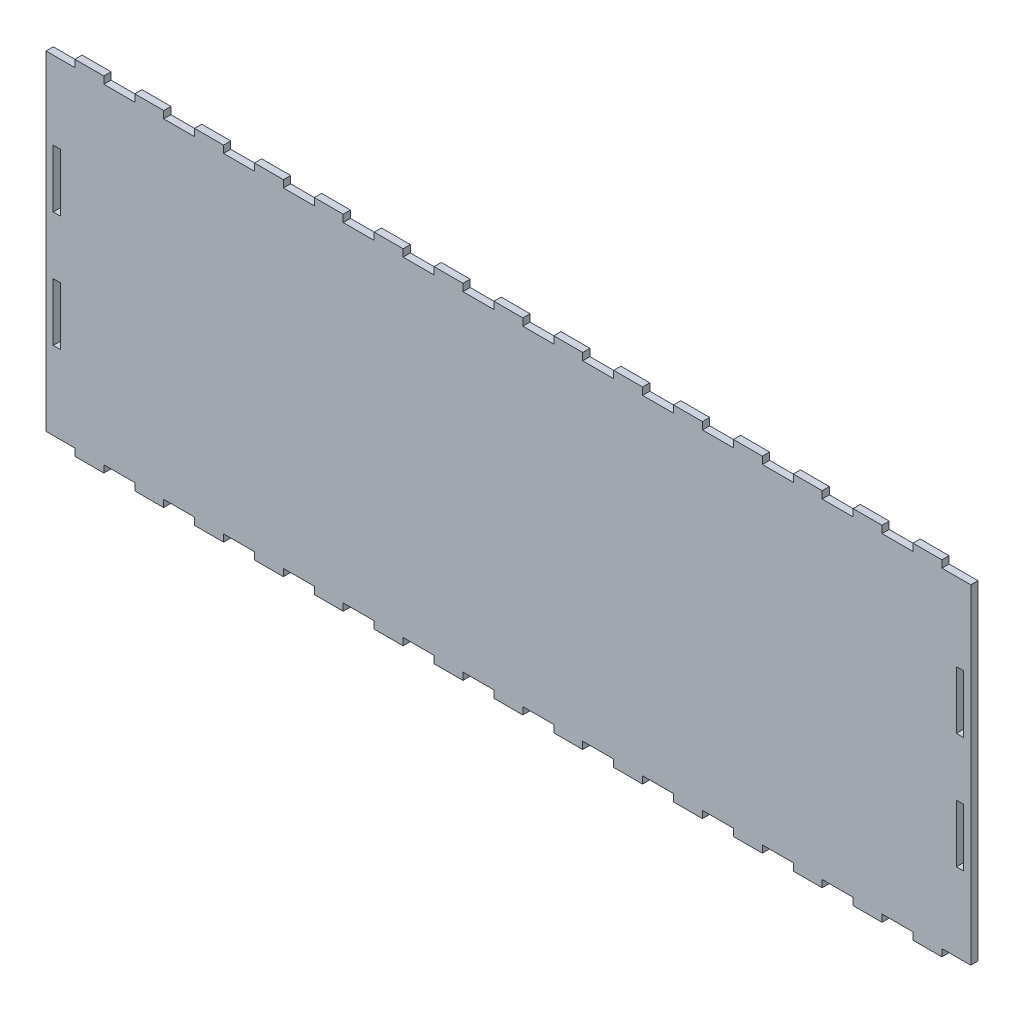
SolidWorks part; units mm, degrees
ref_plane "Front Plane" through (0, 0, 0) normal (0, 0, 1) x (1, 0, 0)
ref_plane "Top Plane" through (0, 0, 0) normal (0, 1, 0) x (1, 0, 0)
ref_plane "Right Plane" through (0, 0, 0) normal (1, 0, 0) x (0, 0, -1)
sketch "Sketch1" plane through (0, 0, 0) normal (0, 0, 1) x (1, 0, 0)
  line L8 (400.05, 110.49) -> (400.05, 85.09)
  line L9 (403.225, 110.49) -> (400.05, 110.49)
  line L10 (403.225, 85.09) -> (403.225, 110.49)
  line L11 (400.05, 85.09) -> (403.225, 85.09)
  line L16 (6.35, 34.29) -> (6.35, 59.69)
  line L17 (3.175, 34.29) -> (6.35, 34.29)
  line L18 (3.175, 59.69) -> (3.175, 34.29)
  line L19 (6.35, 59.69) -> (3.175, 59.69)
  line L24 (6.35, 85.09) -> (6.35, 110.49)
  line L25 (3.175, 85.09) -> (6.35, 85.09)
  line L26 (3.175, 110.49) -> (3.175, 85.09)
  line L27 (6.35, 110.49) -> (3.175, 110.49)
  line L32 (400.05, 59.69) -> (400.05, 34.29)
  line L33 (403.225, 59.69) -> (400.05, 59.69)
  line L34 (403.225, 34.29) -> (403.225, 59.69)
  line L35 (400.05, 34.29) -> (403.225, 34.29)
  line L280 (406.4, 0) -> (406.4, 144.78)
  line L281 (406.4, 144.78) -> (393.7, 144.78)
  line L282 (393.7, 144.78) -> (393.7, 147.955)
  line L283 (393.7, 147.955) -> (381, 147.955)
  line L284 (381, 147.955) -> (381, 144.78)
  line L285 (381, 144.78) -> (367.3929, 144.78)
  line L286 (367.3929, 144.78) -> (367.3929, 147.955)
  line L287 (367.3929, 147.955) -> (354.6929, 147.955)
  line L288 (354.6929, 147.955) -> (354.6929, 144.78)
  line L289 (354.6929, 144.78) -> (341.0857, 144.78)
  line L290 (341.0857, 144.78) -> (341.0857, 147.955)
  line L291 (341.0857, 147.955) -> (328.3857, 147.955)
  line L292 (328.3857, 147.955) -> (328.3857, 144.78)
  line L293 (328.3857, 144.78) -> (314.7786, 144.78)
  line L294 (314.7786, 144.78) -> (314.7786, 147.955)
  line L295 (314.7786, 147.955) -> (302.0786, 147.955)
  line L296 (302.0786, 147.955) -> (302.0786, 144.78)
  line L297 (302.0786, 144.78) -> (288.4714, 144.78)
  line L298 (288.4714, 144.78) -> (288.4714, 147.955)
  line L299 (288.4714, 147.955) -> (275.7714, 147.955)
  line L300 (275.7714, 147.955) -> (275.7714, 144.78)
  line L301 (275.7714, 144.78) -> (262.1643, 144.78)
  line L302 (262.1643, 144.78) -> (262.1643, 147.955)
  line L303 (262.1643, 147.955) -> (249.4643, 147.955)
  line L304 (249.4643, 147.955) -> (249.4643, 144.78)
  line L305 (249.4643, 144.78) -> (235.8571, 144.78)
  line L306 (235.8571, 144.78) -> (235.8571, 147.955)
  line L307 (235.8571, 147.955) -> (223.1571, 147.955)
  line L308 (223.1571, 147.955) -> (223.1571, 144.78)
  line L309 (223.1571, 144.78) -> (209.55, 144.78)
  line L310 (209.55, 144.78) -> (209.55, 147.955)
  line L311 (209.55, 147.955) -> (196.85, 147.955)
  line L312 (196.85, 147.955) -> (196.85, 144.78)
  line L313 (196.85, 144.78) -> (183.2429, 144.78)
  line L314 (183.2429, 144.78) -> (183.2429, 147.955)
  line L315 (183.2429, 147.955) -> (170.5429, 147.955)
  line L316 (170.5429, 147.955) -> (170.5429, 144.78)
  line L317 (170.5429, 144.78) -> (156.9357, 144.78)
  line L318 (156.9357, 144.78) -> (156.9357, 147.955)
  line L319 (156.9357, 147.955) -> (144.2357, 147.955)
  line L320 (144.2357, 147.955) -> (144.2357, 144.78)
  line L321 (144.2357, 144.78) -> (130.6286, 144.78)
  line L322 (130.6286, 144.78) -> (130.6286, 147.955)
  line L323 (130.6286, 147.955) -> (117.9286, 147.955)
  line L324 (117.9286, 147.955) -> (117.9286, 144.78)
  line L325 (117.9286, 144.78) -> (104.3214, 144.78)
  line L326 (104.3214, 144.78) -> (104.3214, 147.955)
  line L327 (104.3214, 147.955) -> (91.6214, 147.955)
  line L328 (91.6214, 147.955) -> (91.6214, 144.78)
  line L329 (91.6214, 144.78) -> (78.0143, 144.78)
  line L330 (78.0143, 144.78) -> (78.0143, 147.955)
  line L331 (78.0143, 147.955) -> (65.3143, 147.955)
  line L332 (65.3143, 147.955) -> (65.3143, 144.78)
  line L333 (65.3143, 144.78) -> (51.7071, 144.78)
  line L334 (51.7071, 144.78) -> (51.7071, 147.955)
  line L335 (51.7071, 147.955) -> (39.0071, 147.955)
  line L336 (39.0071, 147.955) -> (39.0071, 144.78)
  line L337 (39.0071, 144.78) -> (25.4, 144.78)
  line L338 (25.4, 144.78) -> (25.4, 147.955)
  line L339 (25.4, 147.955) -> (12.7, 147.955)
  line L340 (12.7, 147.955) -> (12.7, 144.78)
  line L341 (12.7, 144.78) -> (0, 144.78)
  line L342 (0, 144.78) -> (0, 0)
  line L343 (0, 0) -> (12.7, 0)
  line L344 (12.7, 0) -> (12.7, -3.175)
  line L345 (12.7, -3.175) -> (25.4, -3.175)
  line L346 (25.4, -3.175) -> (25.4, 0)
  line L347 (25.4, 0) -> (39.0071, 0)
  line L348 (39.0071, 0) -> (39.0071, -3.175)
  line L349 (39.0071, -3.175) -> (51.7071, -3.175)
  line L350 (51.7071, -3.175) -> (51.7071, 0)
  line L351 (51.7071, 0) -> (65.3143, 0)
  line L352 (65.3143, 0) -> (65.3143, -3.175)
  line L353 (65.3143, -3.175) -> (78.0143, -3.175)
  line L354 (78.0143, -3.175) -> (78.0143, 0)
  line L355 (78.0143, 0) -> (91.6214, 0)
  line L356 (91.6214, 0) -> (91.6214, -3.175)
  line L357 (91.6214, -3.175) -> (104.3214, -3.175)
  line L358 (104.3214, -3.175) -> (104.3214, 0)
  line L359 (104.3214, 0) -> (117.9286, 0)
  line L360 (117.9286, 0) -> (117.9286, -3.175)
  line L361 (117.9286, -3.175) -> (130.6286, -3.175)
  line L362 (130.6286, -3.175) -> (130.6286, 0)
  line L363 (130.6286, 0) -> (144.2357, 0)
  line L364 (144.2357, 0) -> (144.2357, -3.175)
  line L365 (144.2357, -3.175) -> (156.9357, -3.175)
  line L366 (156.9357, -3.175) -> (156.9357, 0)
  line L367 (156.9357, 0) -> (170.5429, 0)
  line L368 (170.5429, 0) -> (170.5429, -3.175)
  line L369 (170.5429, -3.175) -> (183.2429, -3.175)
  line L370 (183.2429, -3.175) -> (183.2429, 0)
  line L371 (183.2429, 0) -> (196.85, 0)
  line L372 (196.85, 0) -> (196.85, -3.175)
  line L373 (196.85, -3.175) -> (209.55, -3.175)
  line L374 (209.55, -3.175) -> (209.55, 0)
  line L375 (209.55, 0) -> (223.1571, 0)
  line L376 (223.1571, 0) -> (223.1571, -3.175)
  line L377 (223.1571, -3.175) -> (235.8571, -3.175)
  line L378 (235.8571, -3.175) -> (235.8571, 0)
  line L379 (235.8571, 0) -> (249.4643, 0)
  line L380 (249.4643, 0) -> (249.4643, -3.175)
  line L381 (249.4643, -3.175) -> (262.1643, -3.175)
  line L382 (262.1643, -3.175) -> (262.1643, 0)
  line L383 (262.1643, 0) -> (275.7714, 0)
  line L384 (275.7714, 0) -> (275.7714, -3.175)
  line L385 (275.7714, -3.175) -> (288.4714, -3.175)
  line L386 (288.4714, -3.175) -> (288.4714, 0)
  line L387 (288.4714, 0) -> (302.0786, 0)
  line L388 (302.0786, 0) -> (302.0786, -3.175)
  line L389 (302.0786, -3.175) -> (314.7786, -3.175)
  line L390 (314.7786, -3.175) -> (314.7786, 0)
  line L391 (314.7786, 0) -> (328.3857, 0)
  line L392 (328.3857, 0) -> (328.3857, -3.175)
  line L393 (328.3857, -3.175) -> (341.0857, -3.175)
  line L394 (341.0857, -3.175) -> (341.0857, 0)
  line L395 (341.0857, 0) -> (354.6929, 0)
  line L396 (354.6929, 0) -> (354.6929, -3.175)
  line L397 (354.6929, -3.175) -> (367.3929, -3.175)
  line L398 (367.3929, -3.175) -> (367.3929, 0)
  line L399 (367.3929, 0) -> (381, 0)
  line L400 (381, 0) -> (381, -3.175)
  line L401 (381, -3.175) -> (393.7, -3.175)
  line L402 (393.7, -3.175) -> (393.7, 0)
  line L403 (393.7, 0) -> (406.4, 0)
extrude "Boss-Extrude1" add sketch "Sketch1" along normal blind 3.175
sketch "DXF" plane through (0, 0, 3.175) normal (0, 0, 1) x (1, 0, 0)
  line L192 (400.1516, 85.1916) -> (403.1234, 85.1916)
  line L193 (403.1234, 85.1916) -> (403.1234, 110.3884)
  line L194 (400.1516, 110.3884) -> (400.1516, 85.1916)
  line L195 (403.1234, 110.3884) -> (400.1516, 110.3884)
  line L196 (400.1516, 85.1916) -> (403.1234, 85.1916)
  line L197 (403.1234, 85.1916) -> (403.1234, 110.3884)
  line L198 (400.1516, 110.3884) -> (400.1516, 85.1916)
  line L199 (403.1234, 110.3884) -> (400.1516, 110.3884)
  line L210 (400.1516, 34.3916) -> (403.1234, 34.3916)
  line L211 (403.1234, 34.3916) -> (403.1234, 59.5884)
  line L212 (403.1234, 59.5884) -> (400.1516, 59.5884)
  line L213 (400.1516, 59.5884) -> (400.1516, 34.3916)
  line L214 (400.1516, 34.3916) -> (403.1234, 34.3916)
  line L215 (403.1234, 34.3916) -> (403.1234, 59.5884)
  line L216 (403.1234, 59.5884) -> (400.1516, 59.5884)
  line L217 (400.1516, 59.5884) -> (400.1516, 34.3916)
  line L292 (3.2766, 85.1916) -> (6.2484, 85.1916)
  line L293 (6.2484, 85.1916) -> (6.2484, 110.3884)
  line L294 (6.2484, 110.3884) -> (3.2766, 110.3884)
  line L295 (3.2766, 110.3884) -> (3.2766, 85.1916)
  line L296 (3.2766, 85.1916) -> (6.2484, 85.1916)
  line L297 (6.2484, 85.1916) -> (6.2484, 110.3884)
  line L298 (6.2484, 110.3884) -> (3.2766, 110.3884)
  line L299 (3.2766, 110.3884) -> (3.2766, 85.1916)
  line L310 (3.0734, 34.1884) -> (6.4516, 34.1884)
  line L311 (6.4516, 34.1884) -> (6.4516, 59.7916)
  line L312 (3.0734, 59.7916) -> (3.0734, 34.1884)
  line L313 (6.4516, 59.7916) -> (3.0734, 59.7916)
  line L314 (3.0734, 34.1884) -> (6.4516, 34.1884)
  line L315 (6.4516, 34.1884) -> (6.4516, 59.7916)
  line L316 (3.0734, 59.7916) -> (3.0734, 34.1884)
  line L317 (6.4516, 59.7916) -> (3.0734, 59.7916)
  line L372 (393.8016, -0.1016) -> (406.5016, -0.1016)
  line L373 (406.5016, -0.1016) -> (406.5016, 144.8816)
  line L374 (406.5016, 144.8816) -> (393.8016, 144.8816)
  line L375 (393.8016, 144.8816) -> (393.8016, 148.0566)
  line L376 (393.8016, 148.0566) -> (380.8984, 148.0566)
  line L377 (380.8984, 148.0566) -> (380.8984, 144.8816)
  line L378 (380.8984, 144.8816) -> (367.4945, 144.8816)
  line L379 (367.4945, 144.8816) -> (367.4945, 148.0566)
  line L380 (367.4945, 148.0566) -> (354.5913, 148.0566)
  line L381 (354.5913, 148.0566) -> (354.5913, 144.8816)
  line L382 (354.5913, 144.8816) -> (341.1873, 144.8816)
  line L383 (341.1873, 144.8816) -> (341.1873, 148.0566)
  line L384 (341.1873, 148.0566) -> (328.2841, 148.0566)
  line L385 (328.2841, 148.0566) -> (328.2841, 144.8816)
  line L386 (328.2841, 144.8816) -> (314.8802, 144.8816)
  line L387 (314.8802, 144.8816) -> (314.8802, 148.0566)
  line L388 (314.8802, 148.0566) -> (301.977, 148.0566)
  line L389 (301.977, 148.0566) -> (301.977, 144.8816)
  line L390 (301.977, 144.8816) -> (288.573, 144.8816)
  line L391 (288.573, 144.8816) -> (288.573, 148.0566)
  line L392 (288.573, 148.0566) -> (275.6698, 148.0566)
  line L393 (275.6698, 148.0566) -> (275.6698, 144.8816)
  line L394 (275.6698, 144.8816) -> (262.2659, 144.8816)
  line L395 (262.2659, 144.8816) -> (262.2659, 148.0566)
  line L396 (262.2659, 148.0566) -> (249.3627, 148.0566)
  line L397 (249.3627, 148.0566) -> (249.3627, 144.8816)
  line L398 (249.3627, 144.8816) -> (235.9587, 144.8816)
  line L399 (235.9587, 144.8816) -> (235.9587, 148.0566)
  line L400 (235.9587, 148.0566) -> (223.0555, 148.0566)
  line L401 (223.0555, 148.0566) -> (223.0555, 144.8816)
  line L402 (223.0555, 144.8816) -> (209.6516, 144.8816)
  line L403 (209.6516, 144.8816) -> (209.6516, 148.0566)
  line L404 (209.6516, 148.0566) -> (196.7484, 148.0566)
  line L405 (196.7484, 148.0566) -> (196.7484, 144.8816)
  line L406 (196.7484, 144.8816) -> (183.3445, 144.8816)
  line L407 (183.3445, 144.8816) -> (183.3445, 148.0566)
  line L408 (183.3445, 148.0566) -> (170.4413, 148.0566)
  line L409 (170.4413, 148.0566) -> (170.4413, 144.8816)
  line L410 (170.4413, 144.8816) -> (157.0373, 144.8816)
  line L411 (157.0373, 144.8816) -> (157.0373, 148.0566)
  line L412 (157.0373, 148.0566) -> (144.1341, 148.0566)
  line L413 (144.1341, 148.0566) -> (144.1341, 144.8816)
  line L414 (144.1341, 144.8816) -> (130.7302, 144.8816)
  line L415 (130.7302, 144.8816) -> (130.7302, 148.0566)
  line L416 (130.7302, 148.0566) -> (117.827, 148.0566)
  line L417 (117.827, 148.0566) -> (117.827, 144.8816)
  line L418 (117.827, 144.8816) -> (104.423, 144.8816)
  line L419 (104.423, 144.8816) -> (104.423, 148.0566)
  line L420 (104.423, 148.0566) -> (91.5198, 148.0566)
  line L421 (91.5198, 148.0566) -> (91.5198, 144.8816)
  line L422 (91.5198, 144.8816) -> (78.1159, 144.8816)
  line L423 (78.1159, 144.8816) -> (78.1159, 148.0566)
  line L424 (78.1159, 148.0566) -> (65.2127, 148.0566)
  line L425 (65.2127, 148.0566) -> (65.2127, 144.8816)
  line L426 (65.2127, 144.8816) -> (51.8087, 144.8816)
  line L427 (51.8087, 144.8816) -> (51.8087, 148.0566)
  line L428 (51.8087, 148.0566) -> (38.9055, 148.0566)
  line L429 (38.9055, 148.0566) -> (38.9055, 144.8816)
  line L430 (38.9055, 144.8816) -> (25.5016, 144.8816)
  line L431 (25.5016, 144.8816) -> (25.5016, 148.0566)
  line L432 (25.5016, 148.0566) -> (12.5984, 148.0566)
  line L433 (12.5984, 148.0566) -> (12.5984, 144.8816)
  line L434 (12.5984, 144.8816) -> (-0.1016, 144.8816)
  line L435 (-0.1016, 144.8816) -> (-0.1016, -0.1016)
  line L436 (-0.1016, -0.1016) -> (12.5984, -0.1016)
  line L437 (12.5984, -0.1016) -> (12.5984, -3.2766)
  line L438 (12.5984, -3.2766) -> (25.5016, -3.2766)
  line L439 (25.5016, -3.2766) -> (25.5016, -0.1016)
  line L440 (25.5016, -0.1016) -> (38.9055, -0.1016)
  line L441 (38.9055, -0.1016) -> (38.9055, -3.2766)
  line L442 (38.9055, -3.2766) -> (51.8087, -3.2766)
  line L443 (51.8087, -3.2766) -> (51.8087, -0.1016)
  line L444 (51.8087, -0.1016) -> (65.2127, -0.1016)
  line L445 (65.2127, -0.1016) -> (65.2127, -3.2766)
  line L446 (65.2127, -3.2766) -> (78.1159, -3.2766)
  line L447 (78.1159, -3.2766) -> (78.1159, -0.1016)
  line L448 (78.1159, -0.1016) -> (91.5198, -0.1016)
  line L449 (91.5198, -0.1016) -> (91.5198, -3.2766)
  line L450 (91.5198, -3.2766) -> (104.423, -3.2766)
  line L451 (104.423, -3.2766) -> (104.423, -0.1016)
  line L452 (104.423, -0.1016) -> (117.827, -0.1016)
  line L453 (117.827, -0.1016) -> (117.827, -3.2766)
  line L454 (117.827, -3.2766) -> (130.7302, -3.2766)
  line L455 (130.7302, -3.2766) -> (130.7302, -0.1016)
  line L456 (130.7302, -0.1016) -> (144.1341, -0.1016)
  line L457 (144.1341, -0.1016) -> (144.1341, -3.2766)
  line L458 (144.1341, -3.2766) -> (157.0373, -3.2766)
  line L459 (157.0373, -3.2766) -> (157.0373, -0.1016)
  line L460 (157.0373, -0.1016) -> (170.4413, -0.1016)
  line L461 (170.4413, -0.1016) -> (170.4413, -3.2766)
  line L462 (170.4413, -3.2766) -> (183.3445, -3.2766)
  line L463 (183.3445, -3.2766) -> (183.3445, -0.1016)
  line L464 (183.3445, -0.1016) -> (196.7484, -0.1016)
  line L465 (196.7484, -0.1016) -> (196.7484, -3.2766)
  line L466 (196.7484, -3.2766) -> (209.6516, -3.2766)
  line L467 (209.6516, -3.2766) -> (209.6516, -0.1016)
  line L468 (209.6516, -0.1016) -> (223.0555, -0.1016)
  line L469 (223.0555, -0.1016) -> (223.0555, -3.2766)
  line L470 (223.0555, -3.2766) -> (235.9587, -3.2766)
  line L471 (235.9587, -3.2766) -> (235.9587, -0.1016)
  line L472 (235.9587, -0.1016) -> (249.3627, -0.1016)
  line L473 (249.3627, -0.1016) -> (249.3627, -3.2766)
  line L474 (249.3627, -3.2766) -> (262.2659, -3.2766)
  line L475 (262.2659, -3.2766) -> (262.2659, -0.1016)
  line L476 (262.2659, -0.1016) -> (275.6698, -0.1016)
  line L477 (275.6698, -0.1016) -> (275.6698, -3.2766)
  line L478 (275.6698, -3.2766) -> (288.573, -3.2766)
  line L479 (288.573, -3.2766) -> (288.573, -0.1016)
  line L480 (288.573, -0.1016) -> (301.977, -0.1016)
  line L481 (301.977, -0.1016) -> (301.977, -3.2766)
  line L482 (301.977, -3.2766) -> (314.8802, -3.2766)
  line L483 (314.8802, -3.2766) -> (314.8802, -0.1016)
  line L484 (314.8802, -0.1016) -> (328.2841, -0.1016)
  line L485 (328.2841, -0.1016) -> (328.2841, -3.2766)
  line L486 (328.2841, -3.2766) -> (341.1873, -3.2766)
  line L487 (341.1873, -3.2766) -> (341.1873, -0.1016)
  line L488 (341.1873, -0.1016) -> (354.5913, -0.1016)
  line L489 (354.5913, -0.1016) -> (354.5913, -3.2766)
  line L490 (354.5913, -3.2766) -> (367.4945, -3.2766)
  line L491 (367.4945, -3.2766) -> (367.4945, -0.1016)
  line L492 (367.4945, -0.1016) -> (380.8984, -0.1016)
  line L493 (380.8984, -0.1016) -> (380.8984, -3.2766)
  line L494 (380.8984, -3.2766) -> (393.8016, -3.2766)
  line L495 (393.8016, -3.2766) -> (393.8016, -0.1016)
  line L496 (393.8016, -0.1016) -> (406.5016, -0.1016)
  line L497 (406.5016, -0.1016) -> (406.5016, 144.8816)
  line L498 (406.5016, 144.8816) -> (393.8016, 144.8816)
  line L499 (393.8016, 144.8816) -> (393.8016, 148.0566)
  line L500 (393.8016, 148.0566) -> (380.8984, 148.0566)
  line L501 (380.8984, 148.0566) -> (380.8984, 144.8816)
  line L502 (380.8984, 144.8816) -> (367.4945, 144.8816)
  line L503 (367.4945, 144.8816) -> (367.4945, 148.0566)
  line L504 (367.4945, 148.0566) -> (354.5913, 148.0566)
  line L505 (354.5913, 148.0566) -> (354.5913, 144.8816)
  line L506 (354.5913, 144.8816) -> (341.1873, 144.8816)
  line L507 (341.1873, 144.8816) -> (341.1873, 148.0566)
  line L508 (341.1873, 148.0566) -> (328.2841, 148.0566)
  line L509 (328.2841, 148.0566) -> (328.2841, 144.8816)
  line L510 (328.2841, 144.8816) -> (314.8802, 144.8816)
  line L511 (314.8802, 144.8816) -> (314.8802, 148.0566)
  line L512 (314.8802, 148.0566) -> (301.977, 148.0566)
  line L513 (301.977, 148.0566) -> (301.977, 144.8816)
  line L514 (301.977, 144.8816) -> (288.573, 144.8816)
  line L515 (288.573, 144.8816) -> (288.573, 148.0566)
  line L516 (288.573, 148.0566) -> (275.6698, 148.0566)
  line L517 (275.6698, 148.0566) -> (275.6698, 144.8816)
  line L518 (275.6698, 144.8816) -> (262.2659, 144.8816)
  line L519 (262.2659, 144.8816) -> (262.2659, 148.0566)
  line L520 (262.2659, 148.0566) -> (249.3627, 148.0566)
  line L521 (249.3627, 148.0566) -> (249.3627, 144.8816)
  line L522 (249.3627, 144.8816) -> (235.9587, 144.8816)
  line L523 (235.9587, 144.8816) -> (235.9587, 148.0566)
  line L524 (235.9587, 148.0566) -> (223.0555, 148.0566)
  line L525 (223.0555, 148.0566) -> (223.0555, 144.8816)
  line L526 (223.0555, 144.8816) -> (209.6516, 144.8816)
  line L527 (209.6516, 144.8816) -> (209.6516, 148.0566)
  line L528 (209.6516, 148.0566) -> (196.7484, 148.0566)
  line L529 (196.7484, 148.0566) -> (196.7484, 144.8816)
  line L530 (196.7484, 144.8816) -> (183.3445, 144.8816)
  line L531 (183.3445, 144.8816) -> (183.3445, 148.0566)
  line L532 (183.3445, 148.0566) -> (170.4413, 148.0566)
  line L533 (170.4413, 148.0566) -> (170.4413, 144.8816)
  line L534 (170.4413, 144.8816) -> (157.0373, 144.8816)
  line L535 (157.0373, 144.8816) -> (157.0373, 148.0566)
  line L536 (157.0373, 148.0566) -> (144.1341, 148.0566)
  line L537 (144.1341, 148.0566) -> (144.1341, 144.8816)
  line L538 (144.1341, 144.8816) -> (130.7302, 144.8816)
  line L539 (130.7302, 144.8816) -> (130.7302, 148.0566)
  line L540 (130.7302, 148.0566) -> (117.827, 148.0566)
  line L541 (117.827, 148.0566) -> (117.827, 144.8816)
  line L542 (117.827, 144.8816) -> (104.423, 144.8816)
  line L543 (104.423, 144.8816) -> (104.423, 148.0566)
  line L544 (104.423, 148.0566) -> (91.5198, 148.0566)
  line L545 (91.5198, 148.0566) -> (91.5198, 144.8816)
  line L546 (91.5198, 144.8816) -> (78.1159, 144.8816)
  line L547 (78.1159, 144.8816) -> (78.1159, 148.0566)
  line L548 (78.1159, 148.0566) -> (65.2127, 148.0566)
  line L549 (65.2127, 148.0566) -> (65.2127, 144.8816)
  line L550 (65.2127, 144.8816) -> (51.8087, 144.8816)
  line L551 (51.8087, 144.8816) -> (51.8087, 148.0566)
  line L552 (51.8087, 148.0566) -> (38.9055, 148.0566)
  line L553 (38.9055, 148.0566) -> (38.9055, 144.8816)
  line L554 (38.9055, 144.8816) -> (25.5016, 144.8816)
  line L555 (25.5016, 144.8816) -> (25.5016, 148.0566)
  line L556 (25.5016, 148.0566) -> (12.5984, 148.0566)
  line L557 (12.5984, 148.0566) -> (12.5984, 144.8816)
  line L558 (12.5984, 144.8816) -> (-0.1016, 144.8816)
  line L559 (-0.1016, 144.8816) -> (-0.1016, -0.1016)
  line L560 (-0.1016, -0.1016) -> (12.5984, -0.1016)
  line L561 (12.5984, -0.1016) -> (12.5984, -3.2766)
  line L562 (12.5984, -3.2766) -> (25.5016, -3.2766)
  line L563 (25.5016, -3.2766) -> (25.5016, -0.1016)
  line L564 (25.5016, -0.1016) -> (38.9055, -0.1016)
  line L565 (38.9055, -0.1016) -> (38.9055, -3.2766)
  line L566 (38.9055, -3.2766) -> (51.8087, -3.2766)
  line L567 (51.8087, -3.2766) -> (51.8087, -0.1016)
  line L568 (51.8087, -0.1016) -> (65.2127, -0.1016)
  line L569 (65.2127, -0.1016) -> (65.2127, -3.2766)
  line L570 (65.2127, -3.2766) -> (78.1159, -3.2766)
  line L571 (78.1159, -3.2766) -> (78.1159, -0.1016)
  line L572 (78.1159, -0.1016) -> (91.5198, -0.1016)
  line L573 (91.5198, -0.1016) -> (91.5198, -3.2766)
  line L574 (91.5198, -3.2766) -> (104.423, -3.2766)
  line L575 (104.423, -3.2766) -> (104.423, -0.1016)
  line L576 (104.423, -0.1016) -> (117.827, -0.1016)
  line L577 (117.827, -0.1016) -> (117.827, -3.2766)
  line L578 (117.827, -3.2766) -> (130.7302, -3.2766)
  line L579 (130.7302, -3.2766) -> (130.7302, -0.1016)
  line L580 (130.7302, -0.1016) -> (144.1341, -0.1016)
  line L581 (144.1341, -0.1016) -> (144.1341, -3.2766)
  line L582 (144.1341, -3.2766) -> (157.0373, -3.2766)
  line L583 (157.0373, -3.2766) -> (157.0373, -0.1016)
  line L584 (157.0373, -0.1016) -> (170.4413, -0.1016)
  line L585 (170.4413, -0.1016) -> (170.4413, -3.2766)
  line L586 (170.4413, -3.2766) -> (183.3445, -3.2766)
  line L587 (183.3445, -3.2766) -> (183.3445, -0.1016)
  line L588 (183.3445, -0.1016) -> (196.7484, -0.1016)
  line L589 (196.7484, -0.1016) -> (196.7484, -3.2766)
  line L590 (196.7484, -3.2766) -> (209.6516, -3.2766)
  line L591 (209.6516, -3.2766) -> (209.6516, -0.1016)
  line L592 (209.6516, -0.1016) -> (223.0555, -0.1016)
  line L593 (223.0555, -0.1016) -> (223.0555, -3.2766)
  line L594 (223.0555, -3.2766) -> (235.9587, -3.2766)
  line L595 (235.9587, -3.2766) -> (235.9587, -0.1016)
  line L596 (235.9587, -0.1016) -> (249.3627, -0.1016)
  line L597 (249.3627, -0.1016) -> (249.3627, -3.2766)
  line L598 (249.3627, -3.2766) -> (262.2659, -3.2766)
  line L599 (262.2659, -3.2766) -> (262.2659, -0.1016)
  line L600 (262.2659, -0.1016) -> (275.6698, -0.1016)
  line L601 (275.6698, -0.1016) -> (275.6698, -3.2766)
  line L602 (275.6698, -3.2766) -> (288.573, -3.2766)
  line L603 (288.573, -3.2766) -> (288.573, -0.1016)
  line L604 (288.573, -0.1016) -> (301.977, -0.1016)
  line L605 (301.977, -0.1016) -> (301.977, -3.2766)
  line L606 (301.977, -3.2766) -> (314.8802, -3.2766)
  line L607 (314.8802, -3.2766) -> (314.8802, -0.1016)
  line L608 (314.8802, -0.1016) -> (328.2841, -0.1016)
  line L609 (328.2841, -0.1016) -> (328.2841, -3.2766)
  line L610 (328.2841, -3.2766) -> (341.1873, -3.2766)
  line L611 (341.1873, -3.2766) -> (341.1873, -0.1016)
  line L612 (341.1873, -0.1016) -> (354.5913, -0.1016)
  line L613 (354.5913, -0.1016) -> (354.5913, -3.2766)
  line L614 (354.5913, -3.2766) -> (367.4945, -3.2766)
  line L615 (367.4945, -3.2766) -> (367.4945, -0.1016)
  line L616 (367.4945, -0.1016) -> (380.8984, -0.1016)
  line L617 (380.8984, -0.1016) -> (380.8984, -3.2766)
  line L618 (380.8984, -3.2766) -> (393.8016, -3.2766)
  line L619 (393.8016, -3.2766) -> (393.8016, -0.1016)
  dimension "D1" = 0.1016
  dimension "D2" = 0.1016
  dimension "D3" = 0.1016
  dimension "D4" = 0.1016
  dimension "D5" = 0.1016
extrude "DXF-Extrude" [suppressed] add sketch "DXF" against normal blind 3.175
